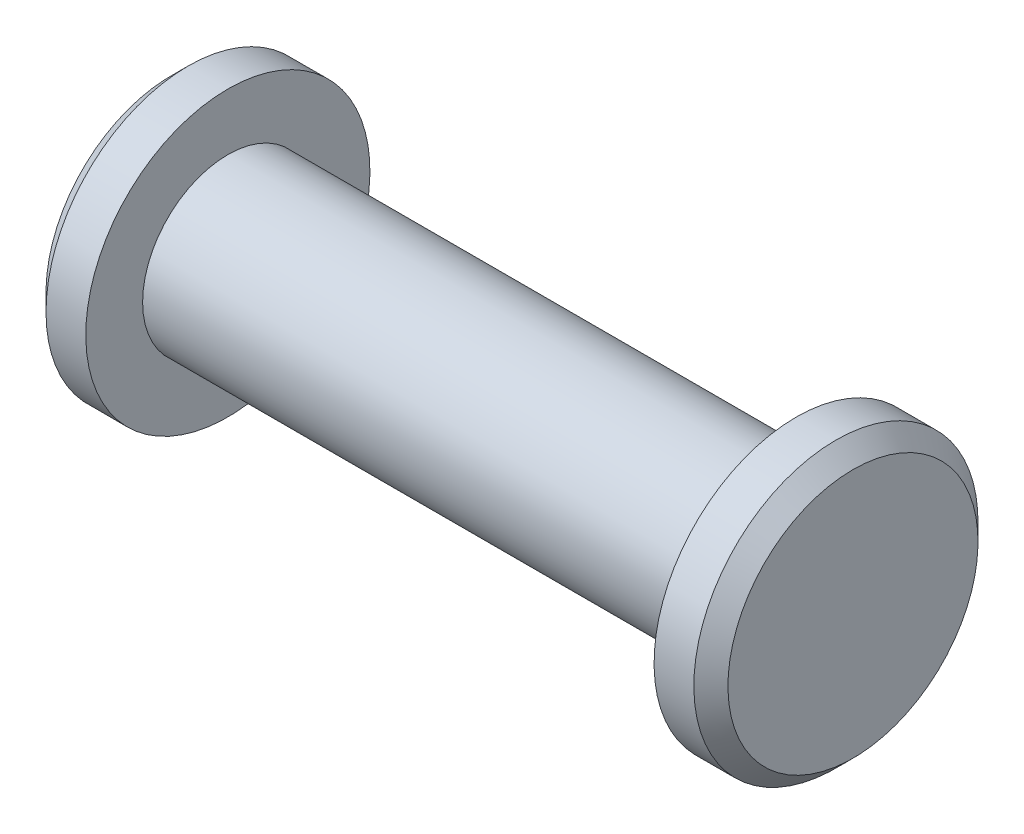
SolidWorks part; units mm, degrees
ref_plane "Front Plane" through (0, 0, 0) normal (0, 0, 1) x (1, 0, 0)
ref_plane "Top Plane" through (0, 0, 0) normal (0, 1, 0) x (1, 0, 0)
ref_plane "Right Plane" through (0, 0, 0) normal (1, 0, 0) x (0, 0, -1)
sketch "Sketch1" plane through (0, 0, 0) normal (0, 0, 1) x (1, 0, 0)
  line L0 (0, 0) -> (-120, 0)
  line L1 (-120, 0) -> (-120, 25)
  line L2 (-120, 25) -> (-110, 25)
  line L3 (-110, 25) -> (-110, 15)
  line L4 (-110, 15) -> (-10, 15)
  line L5 (-10, 15) -> (-10, 25)
  line L6 (-10, 25) -> (0, 25)
  line L7 (0, 25) -> (0, 0)
  dimension "D1" = 10
  dimension "D2" = 100
  dimension "D3" = 10
  dimension "D4" = 15
  dimension "D5" = 25
revolve "Revolve1" add sketch "Sketch1" angle 360 about L0
chamfer "Chamfer1" distance 3 angle 45 2 edges at (-120, 25, 0) (0, 25, 0)
